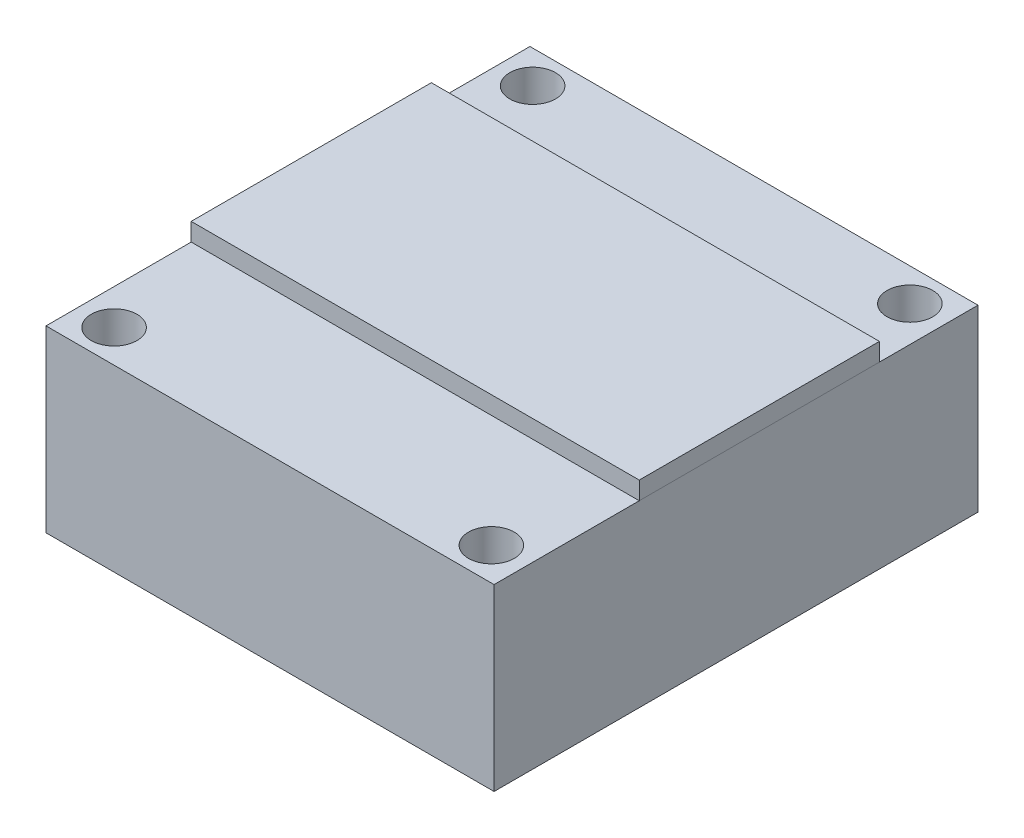
SolidWorks part; units mm, degrees
ref_plane "Front Plane" through (0, 0, 0) normal (0, 0, 1) x (1, 0, 0)
ref_plane "Top Plane" through (0, 0, 0) normal (0, 1, 0) x (1, 0, 0)
ref_plane "Right Plane" through (0, 0, 0) normal (1, 0, 0) x (0, 0, -1)
sketch "Sketch1" plane through (0, 0, 0) normal (0, 1, 0) x (1, 0, 0)
  line L0 (64.6591, -8.8993) -> (64.6591, -47.251) construction
  line L1 (52.1591, -14.8846) -> (77.1591, -14.8846)
  line L2 (52.1591, -14.8846) -> (52.1591, -41.8846)
  line L3 (52.1591, -41.8846) -> (77.1591, -41.8846)
  line L4 (77.1591, -14.8846) -> (77.1591, -41.8846)
  line L5 (52.1591, -14.8846) -> (77.1591, -41.8846) construction
  line L6 (52.1591, -41.8846) -> (77.1591, -14.8846) construction
  line L7 (46.9458, -28.3846) -> (87.2347, -28.3846) construction
  circle A0 centre (54.1341, -16.7096) radius 1.275
  circle A1 centre (54.1341, -40.0596) radius 1.275
  circle A2 centre (75.1841, -40.0596) radius 1.275
  circle A3 centre (75.1841, -16.7096) radius 1.275
  point P0 (64.6591, -28.3846)
  dimension "D3" = 2.55
  dimension "D4" = 0.55
  dimension "D5" = 0.7
  dimension "D1" = 27
  dimension "D2" = 25
extrude "Boss-Extrude1" add sketch "Sketch1" along normal blind 10
sketch "Sketch2" plane through (0, 10, 0) normal (0, 1, 0) x (1, 0, 0)
  line L0 (77.1591, -41.8846) -> (77.1591, -14.8846) construction
  line L1 (52.1591, -33.7846) -> (77.1591, -33.7846)
  line L2 (52.1591, -33.7846) -> (52.1591, -20.3846)
  line L3 (52.1591, -20.3846) -> (77.1591, -20.3846)
  line L4 (77.1591, -33.7846) -> (77.1591, -20.3846)
  line L5 (52.1591, -33.7846) -> (77.1591, -20.3846) construction
  line L6 (52.1591, -20.3846) -> (77.1591, -33.7846) construction
  line L7 (52.1591, -14.8846) -> (52.1591, -41.8846) construction
  line L8 (77.1591, -14.8846) -> (52.1591, -14.8846) construction
  point P0 (64.6591, -27.0846)
  dimension "D1" = 13.4
  dimension "D2" = 5.5
extrude "Boss-Extrude2" add sketch "Sketch2" along normal blind 1 separate body
